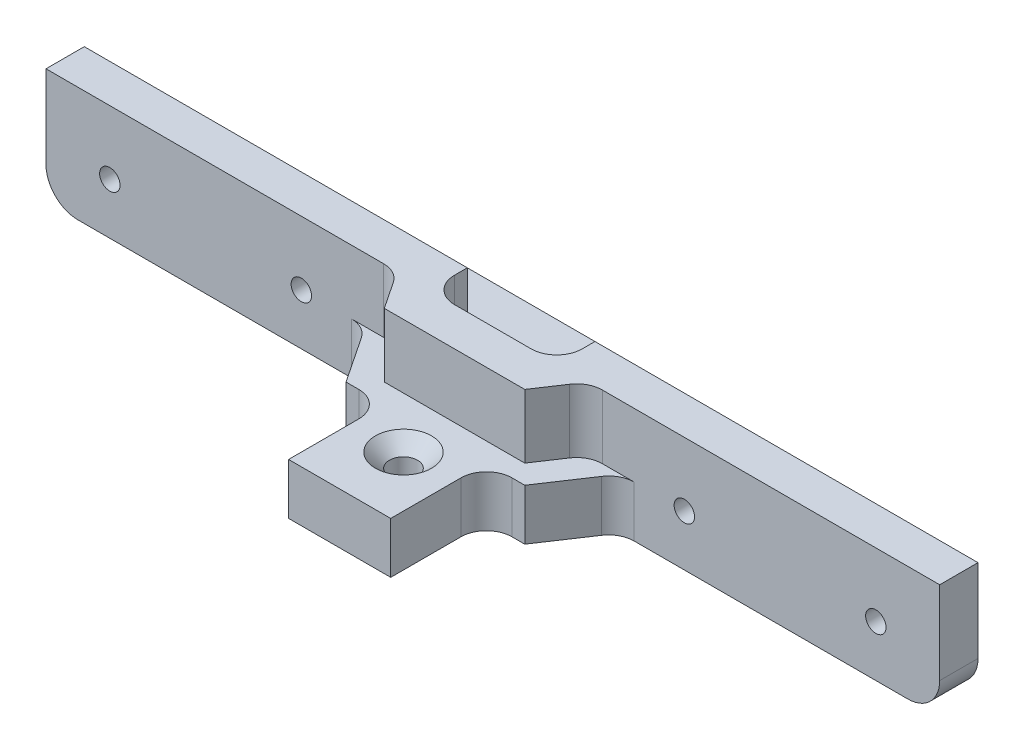
SolidWorks part; units mm, degrees
material "7075-T6 (SN)"
ref_plane "Front Plane" through (0, 0, 0) normal (0, 0, 1) x (1, 0, 0)
ref_plane "Top Plane" through (0, 0, 0) normal (0, 1, 0) x (1, 0, 0)
ref_plane "Right Plane" through (0, 0, 0) normal (1, 0, 0) x (0, 0, -1)
sketch "Sketch1" plane through (0, 0, 0) normal (0, 1, 0) x (1, 0, 0)
  line L14 (-4, 0) -> (4, 0)
  line L15 (4, 0) -> (4, 7.5)
  line L16 (4, 7.5) -> (7, 7.5)
  line L17 (7, 7.5) -> (10, 12)
  line L18 (10, 12) -> (35, 12)
  line L19 (35, 12) -> (35, 15)
  line L20 (35, 15) -> (10, 15)
  line L21 (10, 15) -> (10, 20)
  line L22 (10, 20) -> (-10, 20)
  line L23 (-10, 20) -> (-10, 15)
  line L24 (-10, 15) -> (-35, 15)
  line L25 (-35, 15) -> (-35, 12)
  line L26 (-35, 12) -> (-10, 12)
  line L28 (-4, 7.5) -> (-4, 0)
  line L29 (-4, 7.5) -> (-7, 7.5)
  line L30 (-7, 7.5) -> (-10, 12)
  point P19 (0, 20)
  dimension "D1" = 70
  dimension "D2" = 8
  dimension "D3" = 20
  dimension "D4" = 20
  dimension "D5" = 5
  dimension "D6" = 7.5
  dimension "D7" = 3
  dimension "D8" = 3
extrude "Boss-Extrude1" add sketch "Sketch1" along normal blind 4
sketch "Sketch2" plane through (0, 4, 0) normal (0, 1, 0) x (1, 0, 0)
  line L1 (-35, 15) -> (35, 15)
  line L2 (-35, 15) -> (-35, 12)
  line L3 (-35, 12) -> (35, 12)
  line L4 (35, 15) -> (35, 12)
extrude "Boss-Extrude2" add sketch "Sketch2" along normal blind 5
hole_wizard "CSK for M2 Countersunk Flat Head Screw1" positions "Sketch3" profile "Sketch4" countersink size "M2" standard "DIN"
sketch "Sketch3" plane through (0, 4, 0) normal (0, 1, 0) x (1, 0, 0)
  line L0 (-4, 0) -> (4, 0) construction
  point P0 (0, 15)
  point P2 (0, 5)
  dimension "D1" = 10
  dimension "D2" = 5
sketch "Sketch4" plane through (0, 4, -15) normal (1, 0, 0) x (0, 0, 1)
  line L0 (0, 0) -> (0, 4)
  line L1 (0, 4) -> (1.1, 4)
  line L2 (1.1, 4) -> (1.1, 1.1)
  line L3 (1.1, 1.1) -> (2.2, 0)
  line L5 (2.2, 0) -> (0, 0)
  line L6 (-1.1, 1.1) -> (-2.2, 0) construction
  line L11 (0, -6.35) -> (0, 107.95) construction
  dimension "Thru Hole Dia." = 2.2
  dimension "Thru Hole Depth" = 4
  dimension "Near C'Sink Dia." = 4.4
  dimension "Near C'Sink Angle" = 90
sketch "Sketch5" plane through (0, 9, 0) normal (0, 1, 0) x (1, 0, 0)
  line L0 (35, 15) -> (-35, 15) construction
  line L1 (-5, 15) -> (5, 15)
  line L2 (-5, 15) -> (-5, 12)
  line L3 (-5, 12) -> (5, 12)
  line L4 (5, 15) -> (5, 12)
  line L5 (-35, 12) -> (35, 12) construction
  point P8 (0, 12)
  dimension "D1" = 10
extrude "Cut-Extrude1" cut sketch "Sketch5" against normal up to surface (5 mm away) up to face at (0, 4, -17.0333)
fillet "Fillet1" radius 2.5 2 edges at (35, 0, -13.5) (-35, 0, -13.5)
hole_wizard "M2 Tapped Hole1" positions "Sketch6" profile "Sketch8" tap size "M2" standard "DIN" end condition up to next
sketch "Sketch6" plane through (0, 0, -15) normal (0, 0, -1) x (-1, 0, 0)
  line L0 (-32.5, 0) -> (-10, 0) construction
  line L1 (-35, 9) -> (-35, 2.5) construction
  line L2 (35, 9) -> (35, 2.5) construction
  point P0 (30, 4)
  point P4 (15, 4)
  point P6 (-15, 4)
  point P8 (-30, 4)
  dimension "D1" = 4
  dimension "D2" = 5
  dimension "D3" = 15
  dimension "D4" = 15
  dimension "D5" = 5
sketch "Sketch8" plane through (-30, 4, -15) normal (1, 0, 0) x (0, 1, 0)
  line L0 (0, 0) -> (0, 3)
  line L1 (0, 3) -> (0.8, 3)
  line L2 (0.8, 3) -> (0.8, 0)
  line L5 (0.8, 0) -> (0, 0)
  line L11 (0, -6.35) -> (0, 107.95) construction
  dimension "Thru Tap Drill Dia." = 1.6
  dimension "Thru Tap Drill Depth" = 3
cosmetic thread "Hole Thread1" parameters "D2"=2
cosmetic thread "Hole Thread2" parameters "D2"=2
cosmetic thread "Hole Thread3" parameters "D2"=2
cosmetic thread "Hole Thread4" parameters "D2"=2
sketch "Sketch9" plane through (0, 4, 0) normal (0, 1, 0) x (1, 0, 0)
  line L0 (-7.5, 12) -> (-5.5, 9)
  line L1 (-10, 12) -> (-5, 12) construction
  line L2 (-5.5, 9) -> (5.5, 9)
  line L3 (5.5, 9) -> (7.5, 12)
  line L4 (5, 12) -> (10, 12) construction
  line L5 (7.5, 12) -> (-7.5, 12)
  line L7 (7, 7.5) -> (10, 12) construction
  line L8 (-10, 12) -> (-7, 7.5) construction
  dimension "D1" = 3
extrude "Boss-Extrude3" add sketch "Sketch9" along normal up to surface (5 mm away) up to face at (-20, 9, -13.5)
fillet "Fillet2" radius 2 8 edges at (7.5, 6.5, -12) (-7.5, 6.5, -12) (-4, 2, -7.5) (-10, 2, -12) (10, 2, -12) (4, 2, -7.5) (-5, 6.5, -12) (5, 6.5, -12)
